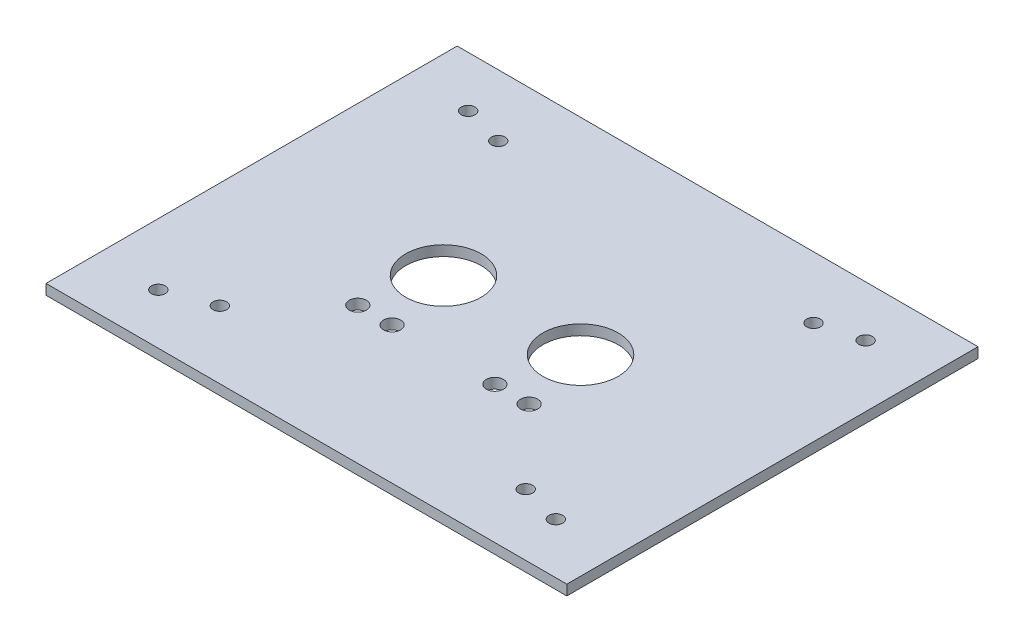
SolidWorks part; units mm, degrees
ref_plane "Front Plane" through (0, 0, 0) normal (0, 0, 1) x (1, 0, 0)
ref_plane "Top Plane" through (0, 0, 0) normal (0, 1, 0) x (1, 0, 0)
ref_plane "Right Plane" through (0, 0, 0) normal (1, 0, 0) x (0, 0, -1)
sketch "Sketch1" plane through (0, 0, 0) normal (0, 1, 0) x (1, 0, 0)
  line L1 (-26.6885, 97.7951) -> (125.3115, 97.7951)
  line L2 (-26.6885, 97.7951) -> (-26.6885, -22.2049)
  line L3 (-26.6885, -22.2049) -> (125.3115, -22.2049)
  line L4 (125.3115, 97.7951) -> (125.3115, -22.2049)
  circle A0 centre (24.3115, 17.7951) radius 2.5
  circle A1 centre (34.3115, 17.7951) radius 2.5
  circle A2 centre (64.3115, 17.7951) radius 2.5
  circle A3 centre (74.3115, 17.7951) radius 2.5
  circle A4 centre (29.3115, 37.7951) radius 11
  circle A5 centre (69.3115, 37.7951) radius 11
  dimension "D3" = 5
  dimension "D6" = 22
  dimension "D1" = 120
  dimension "D2" = 152
  dimension "D4" = 10
  dimension "D5" = 10
  dimension "D7" = 20
  dimension "D8" = 20
  dimension "D9" = 5
  dimension "D10" = 5
  dimension "D11" = 56
  dimension "D12" = 56
  dimension "D13" = 60
  dimension "D14" = 60
extrude "Boss-Extrude1" add sketch "Sketch1" along normal blind 3
sketch "Sketch2" plane through (0, 0, 0) normal (0, -1, 0) x (1, 0, 0)
  circle A1 centre (4.3278, 2.4824) radius 2
  circle A2 centre (95.3115, -79.7951) radius 2
  circle A3 centre (3.3115, -79.7951) radius 2
  circle A4 centre (-8.6885, -82.9971) radius 2
  circle A5 centre (95.3115, 4.2049) radius 2
  circle A6 centre (107.3115, -82.9971) radius 2
  circle A7 centre (3.3115, 4.2049) radius 2 construction
  circle A8 centre (-8.6885, 7.4069) radius 2
  circle A9 centre (107.3115, 7.4069) radius 2
  dimension "D2" = 4
  dimension "D3" = 4
extrude "Cut-Extrude1" cut sketch "Sketch2" against normal through all
